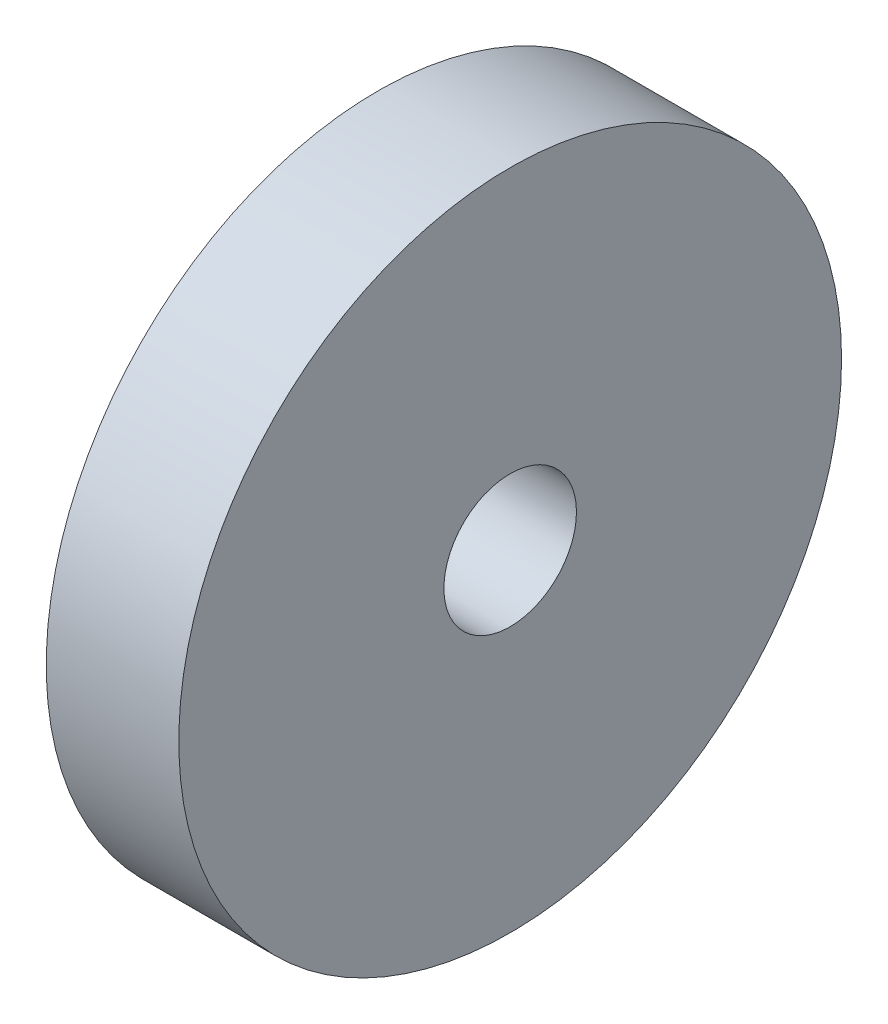
SolidWorks part; units mm, degrees
material "Pine"
ref_plane "Front Plane" through (0, 0, 0) normal (0, 0, 1) x (1, 0, 0)
ref_plane "Top Plane" through (0, 0, 0) normal (0, 1, 0) x (1, 0, 0)
ref_plane "Right Plane" through (0, 0, 0) normal (1, 0, 0) x (0, 0, -1)
sketch "Sketch1" plane through (0, 0, 0) normal (1, 0, 0) x (0, 0, -1)
  circle A0 centre (0, 0) radius 7.5
  dimension "D1" = 15
extrude "Boss-Extrude1" add sketch "Sketch1" along normal blind 3
sketch "Sketch2" plane through (3, 0, 0) normal (1, 0, 0) x (0, 0, -1)
  circle A0 centre (0, 0) radius 1.5
extrude "Cut-Extrude1" cut sketch "Sketch2" against normal through all
